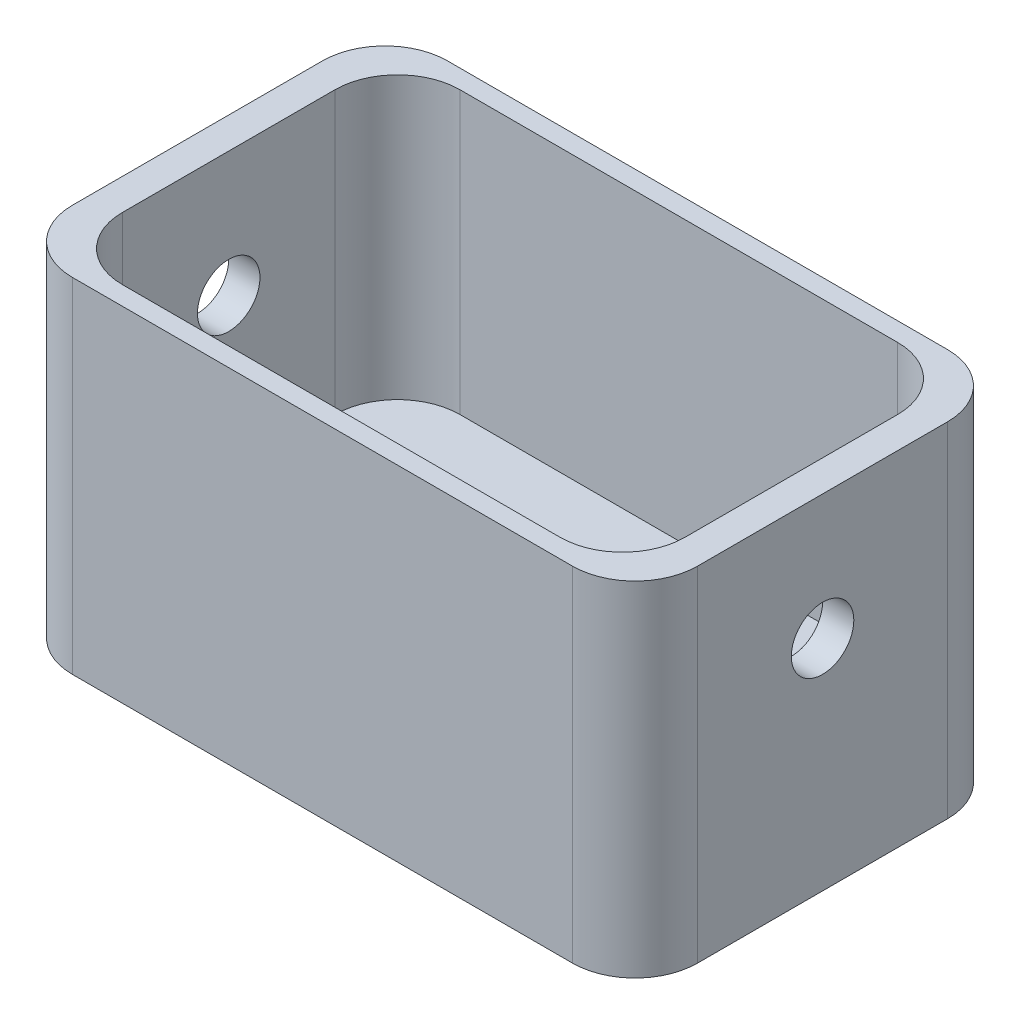
SolidWorks part; units mm, degrees
ref_plane "Plano frontal" through (0, 0, 0) normal (0, 0, 1) x (1, 0, 0)
ref_plane "Plano superior" through (0, 0, 0) normal (0, 1, 0) x (1, 0, 0)
ref_plane "Plano direito" through (0, 0, 0) normal (1, 0, 0) x (0, 0, -1)
sketch "Esboço3" plane through (0, 0, 0) normal (0, 1, 0) x (1, 0, 0)
  line L1 (50, -30) -> (-50, -30)
  line L2 (50, -30) -> (50, 30)
  line L3 (50, 30) -> (-50, 30)
  line L4 (-50, -30) -> (-50, 30)
  line L5 (50, -30) -> (-50, 30) construction
  line L6 (50, 30) -> (-50, -30) construction
  point P0 (0, 0)
  dimension "D1" = 100
  dimension "D2" = 60
extrude "Ressalto-extrusão1" add sketch "Esboço3" along normal blind 55
sketch "Esboço4" plane through (0, 55, 0) normal (0, 1, 0) x (1, 0, 0)
  line L0 (-50, 30) -> (-50, -30) construction
  line L1 (45, 27) -> (-45, 27)
  line L2 (45, 27) -> (45, -27)
  line L3 (45, -27) -> (-45, -27)
  line L4 (-45, 27) -> (-45, -27)
  line L5 (45, 27) -> (-45, -27) construction
  line L6 (45, -27) -> (-45, 27) construction
  line L7 (50, 30) -> (-50, 30) construction
  point P0 (0, 0)
  dimension "D1" = 5
  dimension "D2" = 3
extrude "Corte-extrusão1" cut sketch "Esboço4" against normal blind 45
sketch "Esboço5" plane through (50, 0, 0) normal (1, 0, 0) x (0, 0, -1)
  line L1 (-30, 0) -> (30, 0) construction
  circle A0 centre (0, 35) radius 5
  point P2 (0, 0)
  point P6 (0, 0)
  dimension "D1" = 10
  dimension "D2" = 35
extrude "Corte-extrusão2" cut sketch "Esboço5" against normal blind 100
fillet "Filete1" radius 10 8 edges at (-45, 32.5, 27) (45, 32.5, 27) (45, 32.5, -27) (-45, 32.5, -27) (50, 27.5, 30) (-50, 27.5, 30) (-50, 27.5, -30) (50, 27.5, -30)
